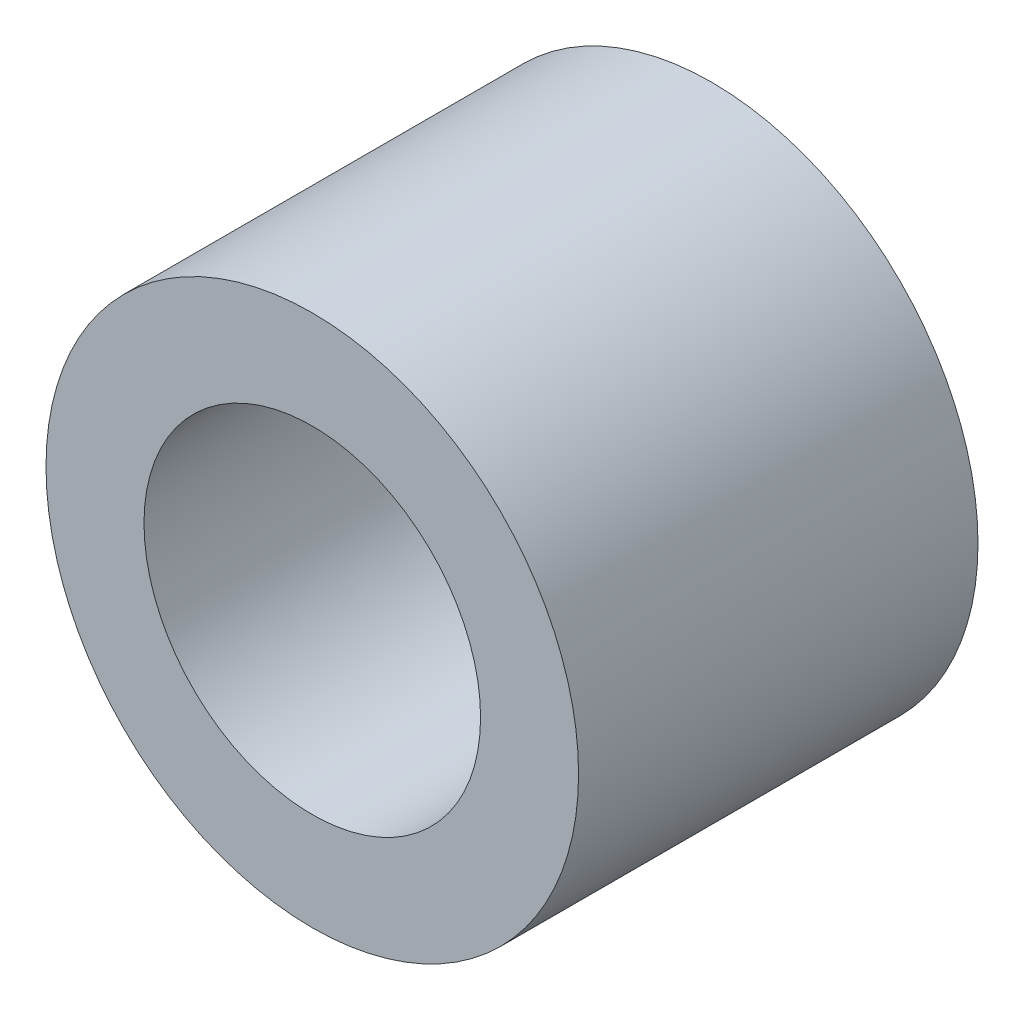
SolidWorks part; units mm, degrees
ref_plane "Front Plane" through (0, 0, 0) normal (0, 0, 1) x (1, 0, 0)
ref_plane "Top Plane" through (0, 0, 0) normal (0, 1, 0) x (1, 0, 0)
ref_plane "Right Plane" through (0, 0, 0) normal (1, 0, 0) x (0, 0, -1)
sketch "Sketch1" plane through (0, 0, 0) normal (0, 0, 1) x (1, 0, 0)
  circle A0 centre (0, 0) radius 6.35
  circle A1 centre (0, 0) radius 4.0132
  dimension "D1" = 12.7
  dimension "ID" = 8.0264
extrude "Extrude1" add sketch "Sketch1" along normal mid plane 9.525
sketch "Sketch2" plane through (0, 0, 0) normal (1, 0, 0) x (0, 0, -1)
  line L0 (-4.7625, -4.0132) -> (4.7625, -4.0132) construction
  line L3 (4.7625, 4.0132) -> (-4.7625, 4.0132) construction
  line L5 (-4.7625, -4.0132) -> (4.7625, -4.0132)
  line L6 (4.7625, 4.0132) -> (-4.7625, 4.0132)
sketch "Sketch4" plane through (0, 0, 4.7625) normal (0, 0, 1) x (1, 0, 0)
  line L0 (0, 0) -> (-2.8378, 2.8378)
  line L1 (0, -6.985) -> (0, 6.985) construction
  circle A0 centre (0, 0) radius 4.0132 construction
  dimension "D1" = 45
